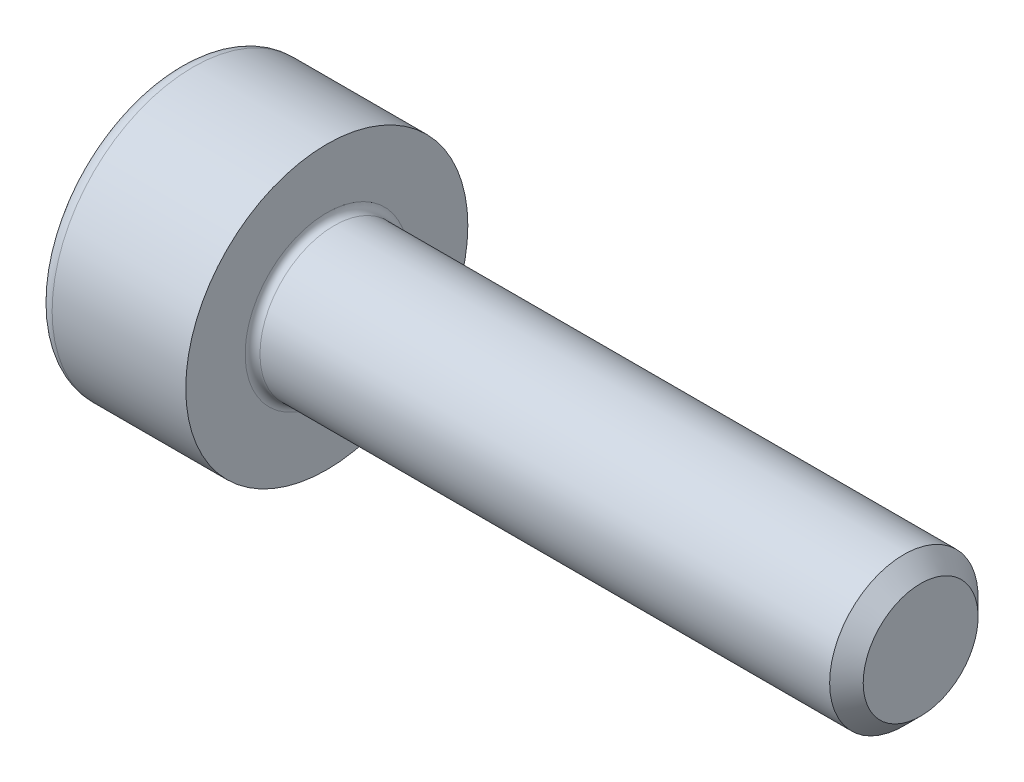
SolidWorks part; units mm, degrees
ref_plane "Plane1" through (0, 0, 0) normal (0, 0, 1) x (1, 0, 0)
ref_plane "Plane2" through (0, 0, 0) normal (0, 1, 0) x (1, 0, 0)
ref_plane "Plane3" through (0, 0, 0) normal (1, 0, 0) x (0, 0, -1)
sketch "BodySke" plane through (0, 0, 0) normal (0, 0, 1) x (1, 0, 0)
  line L0 (0, 0) -> (0, 1.9)
  line L1 (0, 1.9) -> (2, 1.9)
  line L2 (2, 1.9) -> (2, 1)
  line L3 (2, 1) -> (9.774, 1)
  line L4 (10, 0.774) -> (10, 0)
  line L5 (10, 0) -> (0, 0)
  line L6 (-31.75, 0) -> (127, 0) construction
  line L8 (10, 0.774) -> (9.774, 1)
  line L10 (10, -0.774) -> (9.774, -1) construction
  line L11 (2.4, 9.525) -> (2.4, 3.175) construction
  line L12 (2, 9.525) -> (2, 3.175) construction
  line L13 (-50, 9.525) -> (-50, 3.175) construction
  dimension "Diameter" = 2
  dimension "Head_ht" = 2
  dimension "Length" = 8
  dimension "Body_ch_ang" = 45
  dimension "Head_dia" = 3.8
  dimension "Minor_dia" = 1.548
  dimension "Advance" = 0.4
  dimension "Thread_nom" = 8
  dimension "Thread_length" = 60
revolve "Base-Revolve" add sketch "BodySke"
cosmetic thread "ThreadCosmetic"
fillet "Fillet1" radius 0.1 1 edges at (2, 0, 1)
fillet "Fillet2" radius 0.2 1 edges at (0, 0, 1.9)
sketch "Sketch2" plane through (0, 0, 0) normal (0, 0, 1) x (1, 0, 0)
  line L0 (0, 0.76) -> (1, 0.76)
  line L1 (1, 0.76) -> (1.4388, 0)
  line L2 (-31.75, 0) -> (127, 0) construction
  line L3 (1.4388, 0) -> (0, 0)
  line L4 (0, 0) -> (0, 0.76)
  line L6 (0, 0) -> (47.625, 0) construction
  dimension "D1" = 0.76
  dimension "D2" = 60
  dimension "Depth" = 1
revolve "Hex-PreBroach" cut sketch "Sketch2" angle 360 about L6
sketch "Sketch3" plane through (0, 0, 0) normal (-1, 0, 0) x (0, 0.5, 0.866)
  line L0 (0.4388, 0.76) -> (-0.4388, 0.76)
  line L1 (-0.4388, 0.76) -> (-0.8776, 0)
  line L2 (0.4388, 0.76) -> (0.8776, 0)
  line L3 (0.4388, -0.76) -> (0.8776, 0)
  line L4 (0.4388, -0.76) -> (-0.4388, -0.76)
  line L5 (-0.4388, -0.76) -> (-0.8776, 0)
  dimension "D1" = 0.76
  dimension "D2" = 0.76
  dimension "Hex_size" = 1.52
extrude "Hex" cut sketch "Sketch3" against normal blind 1
sketch "ThdSchSke" plane through (0, 0, 0) normal (0, 0, 1) x (1, 0, 0)
  line L0 (3.2, -0.774) -> (3.0418, -1)
  line L1 (3.2, -0.774) -> (3.3582, -1)
  line L2 (3.3582, -1) -> (3.3582, -1.25)
  line L3 (-3.175, 0) -> (5.1513, 0) construction
  line L4 (0, 1.7) -> (0, -1.7) construction
  line L5 (3.3582, -1.25) -> (3.0418, -1.25)
  line L6 (3.0418, -1.25) -> (3.0418, -1)
  dimension "Thread_minor" = 1.548
  dimension "Diameter" = 2
  dimension "Start" = 3.2
  dimension "SideAngle" = 55
  dimension "VeeAngle" = 70
  dimension "Overcut" = 2.5
revolve "ThreadSchematic" [suppressed] cut sketch "ThdSchSke" angle 360 about L3
pattern_linear "ThdSchPat" [suppressed]
equation "\"D2@Sketch3\" = \"Hex_size@Sketch3\" / 2"
equation "\"D1@Sketch3\" = \"Hex_size@Sketch3\" / 2"
equation "\"D1@Sketch2\" = \"Hex_size@Sketch3\" / 2"
equation "\"Thread_minor@ThreadCosmetic\"  =  \"Minor_dia@BodySke\""
equation "\"Depth@Sketch2\" =  \"Key_eng@Hex\""
equation "\"Thread_length@ThreadCosmetic\" = ((sgn( (\"Length@BodySke\" - \"Advance@BodySke\" * 3.0) - \"Thread_nom@BodySke\" )-1)*( (\"Length@BodySke\" - \"Advance@BodySke\" * 3.0) - \"Thread_nom@BodySke\" ))/-2+ \"Thread_nom@BodySke\""
equation "\"Thread_minor@ThdSchSke\" = \"Minor_dia@BodySke\""
equation "\"Diameter@ThdSchSke\" = \"Diameter@BodySke\""
equation "\"Overcut@ThdSchSke\" = \"Diameter@BodySke\" * 1.25"
equation "\"Start@ThdSchSke\" = \"Head_ht@BodySke\" + \"Length@BodySke\" - \"Thread_length@ThreadCosmetic\"  '---Non-countersunk---"
equation "\"Num_threads@ThdSchPat\" = int( \"Thread_length@ThreadCosmetic\" / \"Advance@BodySke\" + 0.999 )  + 1"
equation "\"Advance@ThdSchPat\" = \"Thread_length@ThreadCosmetic\" /  (\"Num_threads@ThdSchPat\" - 1) 'relax it"
equation "\"Num_threads@ThdSchPat\" = \"Num_threads@ThdSchPat\" - sgn( \"Num_threads@ThdSchPat\" - 1) '---chamfered tips only---"
